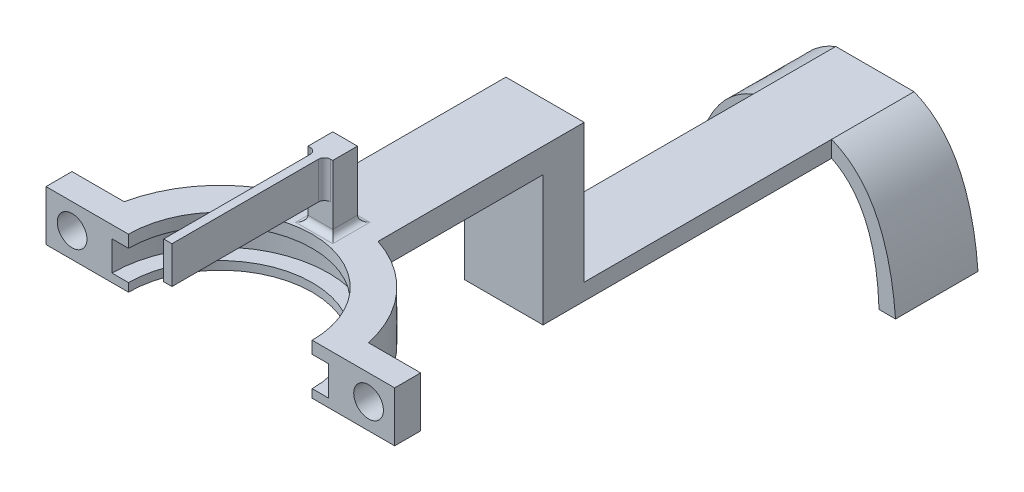
SolidWorks part; units mm, degrees
ref_plane "Front Plane" through (0, 0, 0) normal (0, 0, 1) x (1, 0, 0)
ref_plane "Top Plane" through (0, 0, 0) normal (0, 1, 0) x (1, 0, 0)
ref_plane "Right Plane" through (0, 0, 0) normal (1, 0, 0) x (0, 0, -1)
sketch "Sketch3" plane through (0, 0, 0) normal (0, 0, 1) x (1, 0, 0)
  line L2 (-62.6943, 11.7337) -> (-64.8845, 11.7337)
  line L3 (-62.8845, 10.2507) -> (-60.8845, 10.2507)
  line L5 (-60.8845, 6.6507) -> (-62.8845, 6.6507)
  line L6 (-62.8845, 6.6507) -> (-62.8845, 10.2507)
  line L10 (-64.8845, 11.7337) -> (-64.8845, 5.6398)
  line L11 (-64.8845, 5.6398) -> (-60.8845, 5.6398)
  line L12 (-60.8845, 5.6398) -> (-60.8845, 6.6507)
  line L13 (-60.8845, 10.2507) -> (-60.8845, 11.7337)
  line L14 (-60.8845, 11.7337) -> (-62.6943, 11.7337)
  dimension "D2" = 2
  dimension "D3" = 4
  dimension "D1" = 2
sketch "Sketch4" plane through (0, 0, 0) normal (0, 0, 1) x (1, 0, 0)
  line L0 (-49.7443, 0) -> (-49.7443, 12.8648) construction
  line L1 (27.6543, 0) -> (-27.6543, 0) construction
revolve "Revolve1" add sketch "Sketch3" angle 360 about L0
sketch "Sketch7" plane through (0, 11.7337, 0) normal (0, 1, 0) x (1, 0, 0)
  line L2 (-50.2443, 15.132) -> (-50.2443, 13.1308)
  line L3 (-49.2443, 15.132) -> (-49.2443, 13.1308)
  circle A0 centre (-49.7443, 0) radius 15.1403 construction
  arc A1 (-49.2443, 15.132) -> (-50.2443, 15.132) centre (-49.7443, 0) ccw
  circle A2 centre (-49.7443, 0) radius 13.1403 construction
  arc A3 (-49.2443, 13.1308) -> (-50.2443, 13.1308) centre (-49.7443, 0) ccw
  point P9 (-49.7443, 14.131)
  dimension "D1" = 1
extrude "Boss-Extrude1" add sketch "Sketch7" along normal blind 6.5
sketch "Sketch8" plane through (0, 18.2337, 0) normal (0, 1, 0) x (1, 0, 0)
  line L0 (-50.2443, 15.132) -> (-50.2443, 13.1308) construction
  line L3 (-50.2443, 15.132) -> (-50.2443, 13.1308)
  line L4 (-49.2443, 13.1308) -> (-49.2443, 15.132) construction
  line L5 (-49.2443, 13.1308) -> (-49.2443, 15.132)
  line L6 (-50.2443, 13.1308) -> (-50.2443, -6.3692)
  line L7 (-50.2443, -6.3692) -> (-49.2443, -6.3692)
  line L8 (-49.2443, -6.3692) -> (-49.2443, 13.1308)
  arc A0 (-49.2443, 15.132) -> (-50.2443, 15.132) centre (-49.7443, 0) ccw construction
  arc A1 (-49.2443, 15.132) -> (-50.2443, 15.132) centre (-49.7443, 0) ccw
  dimension "D1" = 19.5
extrude "Boss-Extrude2" add sketch "Sketch8" against normal blind 3
sketch "Sketch9" plane through (0, 11.7337, 0) normal (0, 1, 0) x (1, 0, 0)
  line L2 (-54.4943, 14.3759) -> (-54.4943, 39.3759)
  line L3 (-54.4943, 39.3759) -> (-44.9943, 39.3759)
  line L4 (-44.9943, 39.3759) -> (-44.9943, 14.3759)
  arc A0 (-50.2443, 15.132) -> (-49.2443, 15.132) centre (-49.7443, 0) ccw construction
  arc A1 (-50.2443, 15.132) -> (-54.4943, 14.3759) centre (-49.7443, 0) ccw
  arc A2 (-49.2443, 15.132) -> (-50.2443, 15.132) centre (-49.7443, 0) ccw construction
  arc A3 (-49.2443, 15.132) -> (-50.2443, 15.132) centre (-49.7443, 0) ccw
  arc A4 (-44.9943, 14.3759) -> (-49.2443, 15.132) centre (-49.7443, 0) ccw
  point P9 (-49.7443, 0)
  dimension "D1" = 25
extrude "Boss-Extrude3" add sketch "Sketch9" against normal blind 3
sketch "Sketch10" plane through (0, 8.7337, 0) normal (0, -1, 0) x (1, 0, 0)
  line L0 (-44.9943, -14.3759) -> (-44.9943, -39.3759) construction
  line L1 (-54.4943, -39.3759) -> (-44.9943, -39.3759)
  line L2 (-54.4943, -39.3759) -> (-54.4943, -34.3759)
  line L3 (-54.4943, -34.3759) -> (-44.9943, -34.3759)
  line L4 (-44.9943, -39.3759) -> (-44.9943, -34.3759)
  dimension "D1" = 5
extrude "Boss-Extrude4" add sketch "Sketch10" along normal blind 15.78
sketch "Sketch11" plane through (0, 0, -39.3759) normal (0, 0, -1) x (-1, 0, 0)
  line L0 (54.4943, -7.0463) -> (54.4943, 11.7337) construction
  line L1 (44.9943, -7.0463) -> (54.4943, -7.0463)
  line L2 (44.9943, -7.0463) -> (44.9943, -5.0463)
  line L3 (44.9943, -5.0463) -> (54.4943, -5.0463)
  line L4 (54.4943, -7.0463) -> (54.4943, -5.0463)
  dimension "D1" = 2
extrude "Boss-Extrude5" add sketch "Sketch11" along normal blind 40
sketch "Sketch13" plane through (0, 11.7337, 0) normal (0, 1, 0) x (1, 0, 0)
  line L2 (-49.7443, 3.15) -> (-49.7443, -3.15) construction
  line L3 (-28.604, 3.15) -> (-34.9353, 3.15)
  line L4 (-70.8845, 3.15) -> (-70.8845, -3.15)
  line L5 (-70.8845, -3.15) -> (-64.5532, -3.15)
  line L6 (-28.604, -3.15) -> (-28.604, 3.15)
  line L7 (-64.5532, 3.15) -> (-70.8845, 3.15)
  line L8 (-34.9353, -3.15) -> (-28.604, -3.15)
  arc A0 (-54.4943, 14.3759) -> (-44.9943, 14.3759) centre (-49.7443, 0) ccw construction
  arc A1 (-64.5532, 3.15) -> (-64.5532, -3.15) centre (-49.7443, 0) ccw
  arc A2 (-34.9353, -3.15) -> (-34.9353, 3.15) centre (-49.7443, 0) ccw
  point P10 (-49.7443, 0)
  point P13 (-49.7443, 3.15)
  dimension "D1" = 6.3
extrude "Boss-Extrude6" add sketch "Sketch13" against normal up to surface (6.0939 mm away) up to face at (-49.7443, 5.6398, -11.1403)
sketch "Sketch14" plane through (0, 0, 3.15) normal (0, 0, 1) x (1, 0, 0)
  line L0 (-70.8845, 11.7337) -> (-64.5532, 5.6398) construction
  line L1 (-28.604, 11.7337) -> (-34.9353, 5.6398) construction
  circle A0 centre (-31.7697, 8.6868) radius 1.8
  circle A1 centre (-67.7189, 8.6868) radius 1.8
  dimension "D1" = 3.6
  dimension "D2" = 3.6
extrude "Cut-Extrude1" cut sketch "Sketch14" against normal up to surface (6.3 mm away) contours A1 | A0 up to face at (-67.7189, 8.6868, -3.15)
sketch "Sketch15" plane through (0, 11.7337, 0) normal (0, 1, 0) x (1, 0, 0)
  line L0 (-70.8845, 0) -> (-23.4421, 0) construction
  line L1 (-70.8845, 3.15) -> (-70.8845, -3.15) construction
  line L2 (-7.0756, 0) -> (7.0756, 0) construction
  line L4 (-23.4421, 0) -> (-74.5953, 0)
  line L5 (-23.4421, 0) -> (-23.4421, -21.2106)
  line L6 (-23.4421, -21.2106) -> (-74.5953, -21.2106)
  line L7 (-74.5953, 0) -> (-74.5953, -21.2106)
extrude "Cut-Extrude3" cut sketch "Sketch15" against normal through all
sketch "Sketch16" plane through (0, 0, 0) normal (0, 1, 0) x (1, 0, 0)
  line L1 (-54.8883, 5.4174) -> (-45.2843, 5.4174)
  line L2 (-54.8883, 5.4174) -> (-54.8883, -6.4675)
  line L3 (-54.8883, -6.4675) -> (-45.2843, -6.4675)
  line L4 (-45.2843, 5.4174) -> (-45.2843, -6.4675)
sketch "Sketch18" plane through (0, 11.7337, 0) normal (0, 1, 0) x (1, 0, 0)
  line L0 (-50.2443, 15.132) -> (-49.2443, 15.132) construction
  line L1 (-48.2443, 15.132) -> (-51.2443, 15.132)
  line L2 (-51.2443, 15.132) -> (-51.2443, 12.132)
  line L3 (-51.2443, 12.132) -> (-48.2443, 12.132)
  line L4 (-48.2443, 12.132) -> (-48.2443, 15.132)
  point P7 (-49.7443, 15.132)
  dimension "D1" = 3
  dimension "D2" = 3
extrude "Boss-Extrude7" add sketch "Sketch18" along normal up to surface (6.5 mm away) up to face at (-49.7443, 18.2337, -4.3834)
fillet "Fillet1" radius 0.75 6 edges at (-49.7443, 11.7337, -12.132) (-48.7443, 11.7337, -15.132) (-49.7443, 11.7337, -15.1403) (-50.7443, 11.7337, -15.132) (-51.2443, 11.7337, -13.632) (-48.2443, 11.7337, -13.632)
sketch "Sketch19" plane through (0, 18.2337, 0) normal (0, 1, 0) x (1, 0, 0)
  line L18 (-50.2443, 15.132) -> (-51.2443, 15.132)
  line L19 (-51.2443, 15.132) -> (-51.2443, 12.132)
  line L20 (-51.2443, 12.132) -> (-50.2443, 12.132)
  line L21 (-50.2443, 12.132) -> (-50.2443, -6.3692)
  line L22 (-50.2443, -6.3692) -> (-49.2443, -6.3692)
  line L23 (-49.2443, -6.3692) -> (-49.2443, 12.132)
  line L24 (-49.2443, 12.132) -> (-48.2443, 12.132)
  line L25 (-48.2443, 12.132) -> (-48.2443, 15.132)
  line L26 (-48.2443, 15.132) -> (-49.2443, 15.132)
  line L27 (-50.2443, 15.132) -> (-51.2443, 15.132)
  line L28 (-51.2443, 15.132) -> (-51.2443, 12.132)
  line L29 (-51.2443, 12.132) -> (-50.2443, 12.132)
  line L30 (-50.2443, 12.132) -> (-50.2443, -6.3692)
  line L31 (-50.2443, -6.3692) -> (-49.2443, -6.3692)
  line L32 (-49.2443, -6.3692) -> (-49.2443, 12.132)
  line L33 (-49.2443, 12.132) -> (-48.2443, 12.132)
  line L34 (-48.2443, 12.132) -> (-48.2443, 15.132)
  line L35 (-48.2443, 15.132) -> (-49.2443, 15.132)
  arc A2 (-49.2443, 15.132) -> (-50.2443, 15.132) centre (-49.7443, 0) ccw
  arc A3 (-49.2443, 15.132) -> (-50.2443, 15.132) centre (-49.7443, 0) ccw
  dimension "D1" = 0
extrude "Boss-Extrude8" add sketch "Sketch19" along normal blind 1.5
fillet "Fillet2" radius 0.75 2 edges at (-49.2443, 17.4837, -12.132) (-50.2443, 17.4837, -12.132)
sketch "Sketch20" plane through (0, 0, -79.3759) normal (0, 0, -1) x (-1, 0, 0)
  line L0 (49.7443, -5.0463) -> (49.7443, -6.1882) construction
  line L1 (54.4943, -5.0463) -> (44.9943, -5.0463) construction
  line L2 (62.2443, -20.0463) -> (37.2443, -20.0463) construction
  line L4 (37.2443, -20.0463) -> (39.2443, -20.0463)
  line L5 (60.2443, -20.0463) -> (62.2443, -20.0463)
  line L8 (44.9943, -7.0463) -> (54.4943, -7.0463)
  line L9 (44.9943, -5.0463) -> (54.4943, -5.0463)
  line L11 (54.4943, -5.0463) -> (44.9943, -5.0463) construction
  line L12 (49.7443, -7.0463) -> (49.7443, -20.0463) construction
  spline S0 degree 2 poles (37.2443, -20.0463) (38.1968, -7.7468) (44.9943, -5.0463) knots 0 0 0 0.63993 0.63993 0.63993
  spline S1 degree 2 poles (39.2443, -20.0463) (39.5823, -9.6501) (44.9943, -7.0463) knots 0 0 0 0.599407 0.599407 0.599407
  spline S3 degree 2 poles (62.2443, -20.0463) (61.2918, -7.7468) (54.4943, -5.0463) knots 0 0 0 0.63993 0.63993 0.63993
  spline S4 degree 2 poles (54.4943, -7.0463) (59.9062, -9.6501) (60.2443, -20.0463) knots 0.400593 0.400593 0.400593 1 1 1
  point P7 (49.7443, -20.0463)
  dimension "D3" = 2
  dimension "D1" = 15
  dimension "D2" = 25
  dimension "D4" = 2
extrude "Boss-Extrude9" add sketch "Sketch20" against normal blind 10
